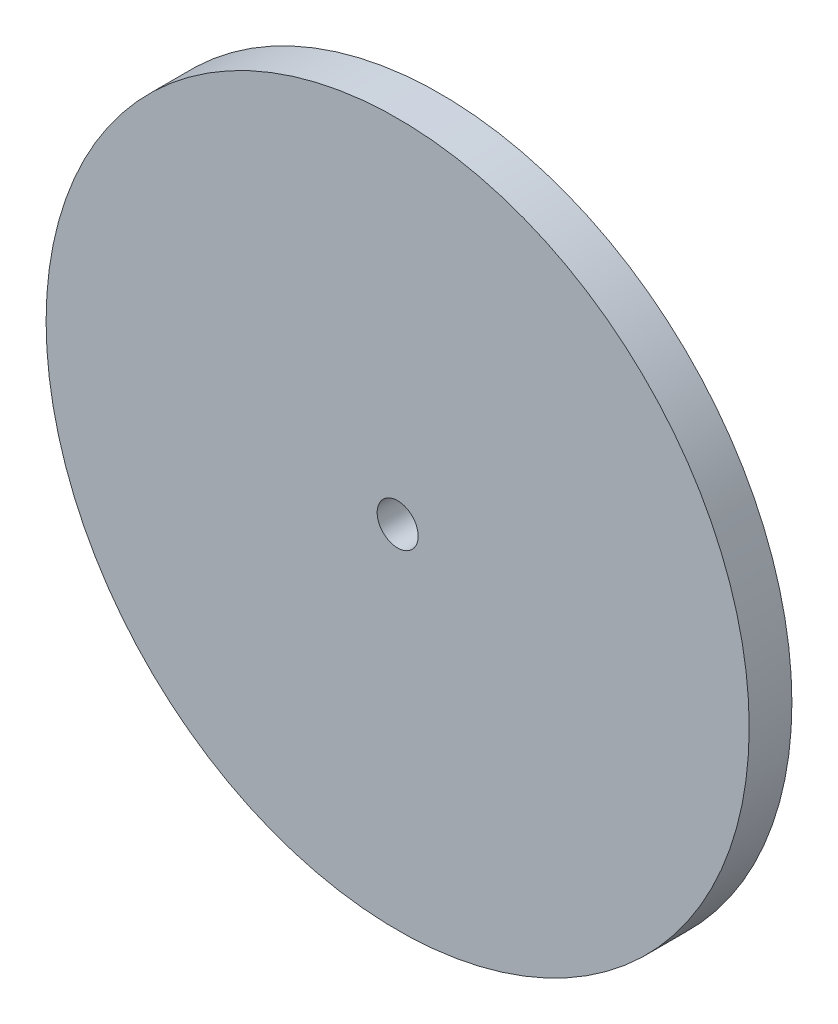
SolidWorks part; units mm, degrees
ref_plane "Front Plane" through (0, 0, 0) normal (0, 0, 1) x (1, 0, 0)
ref_plane "Top Plane" through (0, 0, 0) normal (0, 1, 0) x (1, 0, 0)
ref_plane "Right Plane" through (0, 0, 0) normal (1, 0, 0) x (0, 0, -1)
sketch "Sketch1" plane through (0, 0, 0) normal (0, 0, 1) x (1, 0, 0)
  circle A0 centre (0, 0) radius 41.1623
  circle A1 centre (0, 0) radius 2.4
  dimension "D1" = 82.3246
  dimension "D2" = 4.8
extrude "Boss-Extrude1" add sketch "Sketch1" along normal blind 5
